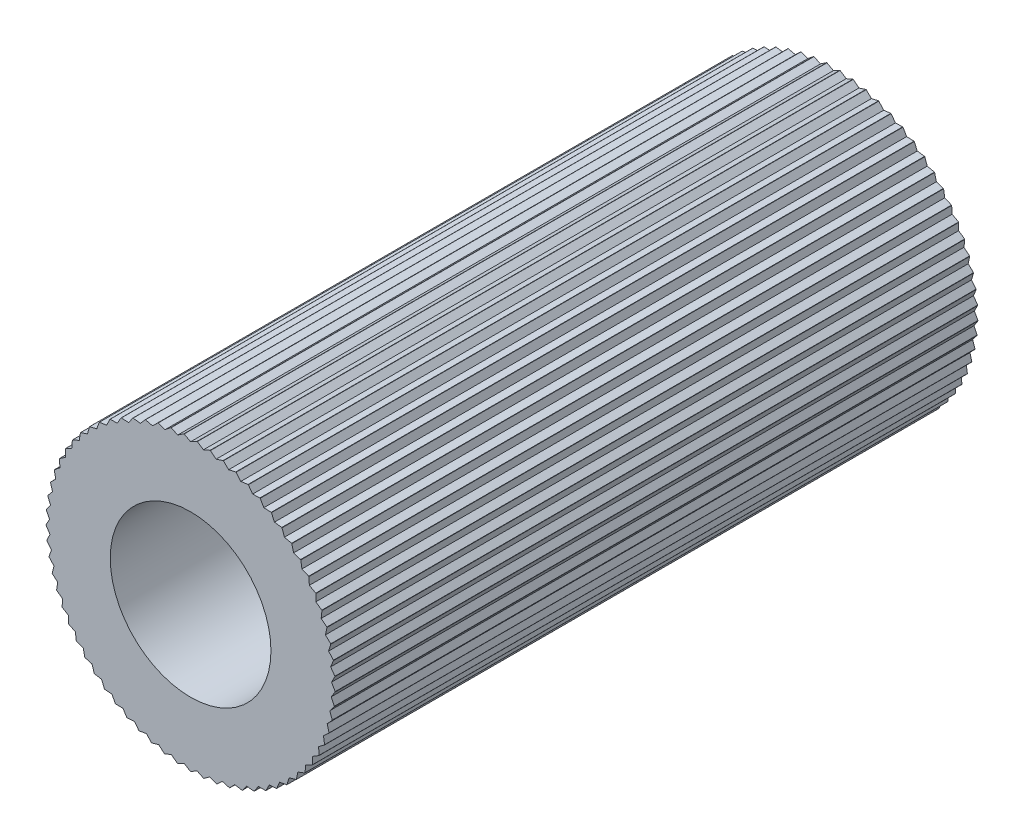
SolidWorks part; units mm, degrees
ref_plane "Alzado" through (0, 0, 0) normal (0, 0, 1) x (1, 0, 0)
ref_plane "Planta" through (0, 0, 0) normal (0, 1, 0) x (1, 0, 0)
ref_plane "Vista lateral" through (0, 0, 0) normal (1, 0, 0) x (0, 0, -1)
sketch "Croquis1" plane through (0, 0, 0) normal (0, 0, 1) x (1, 0, 0)
  circle A0 centre (0, 0) radius 2.25
  dimension "D1" = 4.5
extrude "Saliente-Extruir1" add sketch "Croquis1" along normal blind 10
hole_wizard "Perforador para roscar para macho de roscar para M31" positions "Croquis3" profile "Croquis2" hole size "M3" standard "ISO" end condition through all
sketch "Croquis3" plane through (0, 0, 10) normal (0, 0, 1) x (1, 0, 0)
  point P0 (0, 0)
sketch "Croquis2" plane through (0, 0, 10) normal (1, 0, 0) x (0, -1, 0)
  line L0 (0, 0) -> (0, 10)
  line L1 (0, 10) -> (1.25, 10)
  line L2 (1.25, 10) -> (1.25, 0)
  line L5 (1.25, 0) -> (0, 0)
  line L11 (0, -6.35) -> (0, 107.95) construction
  dimension "Diámetro de taladro hasta el siguiente" = 2.5
  dimension "Profundidad de taladro hasta el siguiente" = 10
sketch "Croquis5" plane through (0, 0, 10) normal (0, 0, 1) x (1, 0, 0)
  line L0 (0, 2.25) -> (0, -2.25) construction
  line L5 (-0.1, 2.2478) -> (0, 2.193)
  line L6 (0, 2.193) -> (0.1, 2.2478)
  circle A0 centre (0, 0) radius 2.25 construction
  arc A1 (0.1, 2.2478) -> (-0.1, 2.2478) centre (0, 0) ccw
extrude "Cortar-Extruir3" cut sketch "Croquis5" against normal blind 10
pattern_circular "MatrizC1" count 69 over 360 about axis through (0, 0, 0) along (0, 0, 1) of "Cortar-Extruir3"
